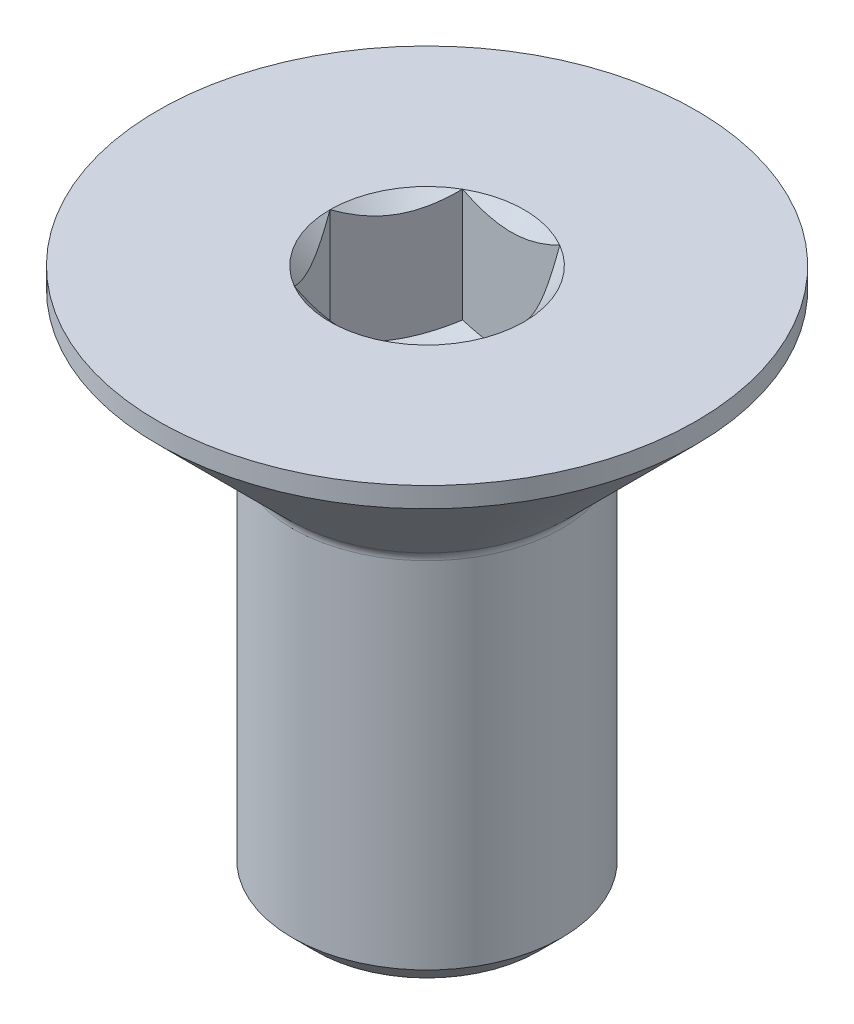
SolidWorks part; units mm, degrees
ref_plane "Plano frontal" through (0, 0, 0) normal (0, 0, 1) x (1, 0, 0)
ref_plane "Plano superior" through (0, 0, 0) normal (0, 1, 0) x (1, 0, 0)
ref_plane "Plano direito" through (0, 0, 0) normal (1, 0, 0) x (0, 0, -1)
sketch "Esboço1" plane through (0, 0, 0) normal (0, 0, 1) x (1, 0, 0)
  line L0 (0, -1000) -> (0, 49000) construction
  line L1 (0, -2.5511) -> (1.25, -1.8)
  line L2 (1.25, -1.8) -> (1.25, 0)
  line L3 (1.25, 0) -> (4, 0)
  line L4 (4, 0) -> (4, -0.3)
  line L5 (4, -0.3) -> (2.0586, -2.2414)
  line L6 (2, -2.3828) -> (2, -7.65)
  line L7 (2, -7.65) -> (1.65, -8)
  line L8 (1.65, -8) -> (0, -8)
  line L9 (0, -8) -> (0, -2.5511)
  arc A0 (2.0586, -2.2414) -> (2, -2.3828) centre (2.2, -2.3828) ccw
  dimension "RAIO_CABEÇA" = 0.2
  dimension "DIAMETRO_SEXTAVADO" = 2.5
  dimension "D2" = 59
  dimension "DIAMETRO_CABECA" = 8
  dimension "ALTURA_FACE" = 0.3
  dimension "ANGULO_PONTA" = 45
  dimension "CHANFRO_PONTA" = 0.35
  dimension "DIAMETRO_CORPO" = 4
  dimension "PROFUNDIDADE_SEXTAVADO" = 1.8
  dimension "COMPRIMENTO" = 8
revolve "Revolução1" add sketch "Esboço1" angle 360 about L0
sketch "Esboço2" plane through (0, 0, 0) normal (0, 1, 0) x (1, 0, 0)
  line L1 (-1.4434, 0) -> (-0.7217, -1.25)
  line L2 (-0.7217, -1.25) -> (0.7217, -1.25)
  line L3 (0.7217, -1.25) -> (1.4434, 0)
  line L4 (1.4434, 0) -> (0.7217, 1.25)
  line L5 (0.7217, 1.25) -> (-0.7217, 1.25)
  line L6 (-0.7217, 1.25) -> (-1.4434, 0)
  circle A0 centre (0, 0) radius 1.25 construction
  circle A1 centre (0, 0) radius 1.25 construction
extrude "Corte-extrusão1" cut sketch "Esboço2" against normal up to surface (1.6838 mm away)
sketch "Esboço3" plane through (0, 0, 0) normal (0, 0, 1) x (1, 0, 0)
  line L0 (0, -1000) -> (0, 49000) construction
  line L1 (1.4434, 0) -> (0, -1.4434)
  line L2 (0, -1.4434) -> (0, 0)
  line L3 (0, 0) -> (1.4434, 0)
  dimension "D1" = 45
revolve "Corte-Revolução1" cut sketch "Esboço3" angle 360 about L0
sketch "Esboço4" plane through (0, 0, 0) normal (0, 0, 1) x (1, 0, 0)
  line L0 (-2, -7) -> (2, -7)
  line L1 (-2, -2.3828) -> (-2, -7.65) construction
  line L2 (2, -7.65) -> (2, -2.3828) construction
  line L3 (-1.65, -8) -> (1.65, -8) construction
  dimension "COMPRIMENTO_ROSCA" = 1
split line "Linha de divisão1" [suppressed]
